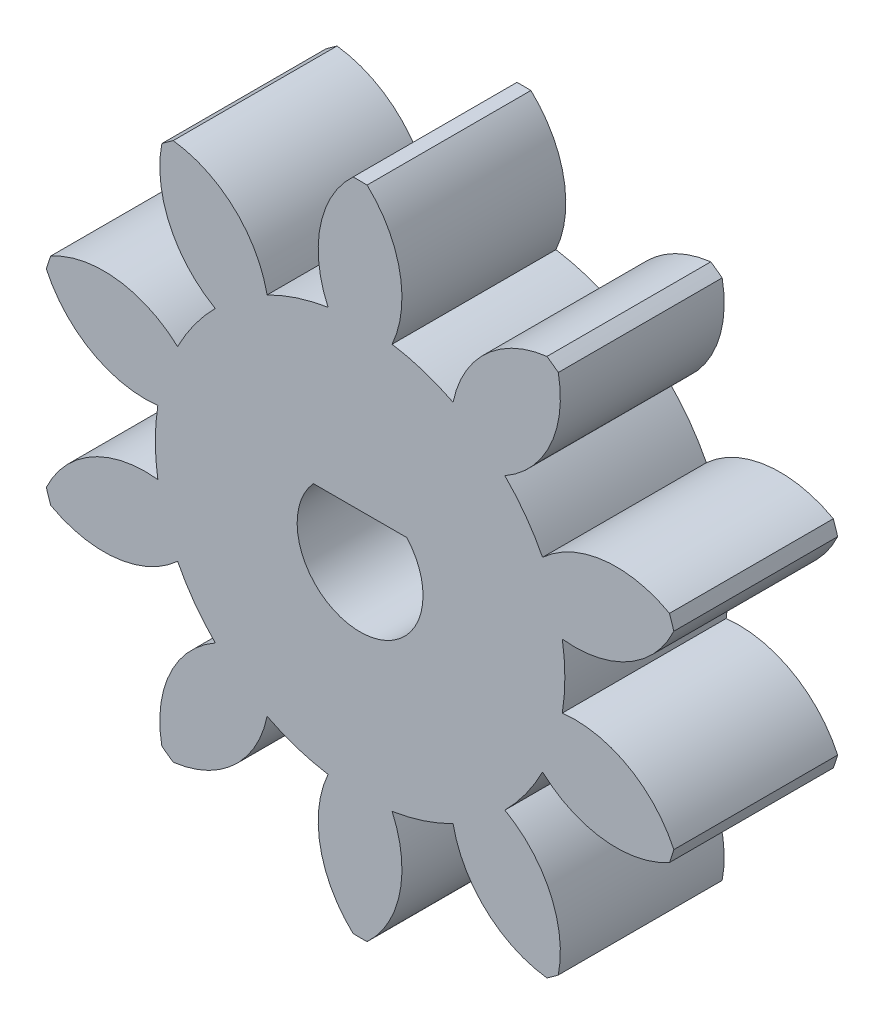
SolidWorks part; units mm, degrees
ref_plane "Front Plane" through (0, 0, 0) normal (0, 0, 1) x (1, 0, 0)
ref_plane "Top Plane" through (0, 0, 0) normal (0, 1, 0) x (1, 0, 0)
ref_plane "Right Plane" through (0, 0, 0) normal (1, 0, 0) x (0, 0, -1)
sketch "Sketch4" plane through (0, 0, 0) normal (0, 0, 1) x (1, 0, 0)
  point P0 (0, 12)
  arc B0 (11.3307, 3.9517) -> (6.6819, 3.404) centre (9.3858, 0.4563) ccw
  arc B1 (6.6819, 3.404) -> (5.3022, 5.303) centre (0, 0) ccw
  arc B2 (5.3022, 5.303) -> (7.2596, 9.555) centre (3.3343, 8.7855) ccw
  arc B3 (7.2596, 9.555) -> (6.844, 9.857) centre (0, 0) ccw
  arc B4 (6.844, 9.857) -> (3.405, 6.6814) centre (7.3251, 5.886) ccw
  arc B5 (3.405, 6.6814) -> (1.1725, 7.4068) centre (0, 0) ccw
  arc B6 (1.1725, 7.4068) -> (0.2569, 11.9973) centre (-2.4664, 9.0675) ccw
  arc B7 (0.2569, 11.9973) -> (-0.2569, 11.9973) centre (0, 0) ccw
  arc B8 (-0.2569, 11.9973) -> (-1.1725, 7.4068) centre (2.4664, 9.0675) ccw
  arc B9 (-1.1725, 7.4068) -> (-3.405, 6.6814) centre (0, 0) ccw
  arc B10 (-3.405, 6.6814) -> (-6.844, 9.857) centre (-7.3251, 5.886) ccw
  arc B11 (-6.844, 9.857) -> (-7.2596, 9.555) centre (0, 0) ccw
  arc B12 (-7.2596, 9.555) -> (-5.3022, 5.303) centre (-3.3343, 8.7855) ccw
  arc B13 (-5.3022, 5.303) -> (-6.6819, 3.404) centre (0, 0) ccw
  arc B14 (-6.6819, 3.404) -> (-11.3307, 3.9517) centre (-9.3858, 0.4563) ccw
  arc B15 (-11.3307, 3.9517) -> (-11.4894, 3.463) centre (0, 0) ccw
  arc B16 (-11.4894, 3.463) -> (-7.4066, 1.1737) centre (-7.8615, 5.1477) ccw
  arc B17 (-7.4066, 1.1737) -> (-7.4066, -1.1737) centre (0, 0) ccw
  arc B18 (-7.4066, -1.1737) -> (-11.4894, -3.463) centre (-7.8615, -5.1477) ccw
  arc B19 (-11.4894, -3.463) -> (-11.3307, -3.9517) centre (0, 0) ccw
  arc B20 (-11.3307, -3.9517) -> (-6.6819, -3.404) centre (-9.3858, -0.4563) ccw
  arc B21 (-6.6819, -3.404) -> (-5.3022, -5.303) centre (0, 0) ccw
  arc B22 (-5.3022, -5.303) -> (-7.2596, -9.555) centre (-3.3343, -8.7855) ccw
  arc B23 (-7.2596, -9.555) -> (-6.844, -9.857) centre (0, 0) ccw
  arc B24 (-6.844, -9.857) -> (-3.405, -6.6814) centre (-7.3251, -5.886) ccw
  arc B25 (-3.405, -6.6814) -> (-1.1725, -7.4068) centre (0, 0) ccw
  arc B26 (-1.1725, -7.4068) -> (-0.2569, -11.9973) centre (2.4664, -9.0675) ccw
  arc B27 (-0.2569, -11.9973) -> (0.2569, -11.9973) centre (0, 0) ccw
  arc B28 (0.2569, -11.9973) -> (1.1725, -7.4068) centre (-2.4664, -9.0675) ccw
  arc B29 (1.1725, -7.4068) -> (3.405, -6.6814) centre (0, 0) ccw
  arc B30 (3.405, -6.6814) -> (6.844, -9.857) centre (7.3251, -5.886) ccw
  arc B31 (6.844, -9.857) -> (7.2596, -9.555) centre (0, 0) ccw
  arc B32 (7.2596, -9.555) -> (5.3022, -5.303) centre (3.3343, -8.7855) ccw
  arc B33 (5.3022, -5.303) -> (6.6819, -3.404) centre (0, 0) ccw
  arc B34 (6.6819, -3.404) -> (11.3307, -3.9517) centre (9.3858, -0.4563) ccw
  arc B35 (11.3307, -3.9517) -> (11.4894, -3.463) centre (0, 0) ccw
  arc B36 (11.4894, -3.463) -> (7.4066, -1.1737) centre (7.8615, -5.1477) ccw
  arc B37 (7.4066, -1.1737) -> (7.4066, 1.1737) centre (0, 0) ccw
  arc B38 (7.4066, 1.1737) -> (11.4894, 3.463) centre (7.8615, 5.1477) ccw
  arc B39 (11.4894, 3.463) -> (11.3307, 3.9517) centre (0, 0) ccw
  circle B40 centre (0, 0) radius 2
sketch_block_instance "Block3-1"
sketch_block "Block3"
extrude "Boss-Extrude3" add sketch "Sketch4" along normal blind 6
sketch "Sketch6" plane through (0, 0, 6) normal (0, 0, 1) x (1, 0, 0)
  circle A0 centre (0, 0) radius 3.2769
extrude "Boss-Extrude4" add sketch "Sketch6" against normal up to surface (6 mm away) up to face at (0, 0, 0)
sketch "Sketch7" plane through (0, 0, 6) normal (0, 0, 1) x (1, 0, 0)
  line L0 (0, 0) -> (0, 1.62) construction
  line L4 (-1.7106, 1.545) -> (1.7106, 1.545)
  arc A0 (-1.7106, 1.545) -> (1.7106, 1.545) centre (0, 0) ccw
  dimension "D2" = 1.545
  dimension "D1" = 2.305
extrude "Cut-Extrude2" cut sketch "Sketch7" against normal blind 10
